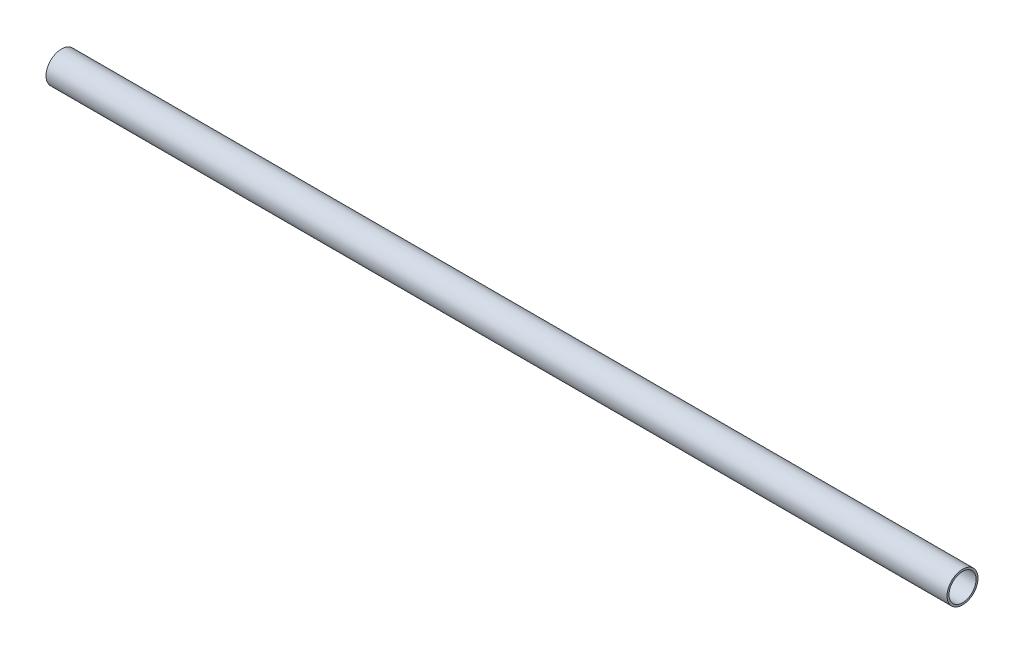
SolidWorks part; units mm, degrees
ref_plane "Ebene vorne" through (0, 0, 0) normal (0, 0, 1) x (1, 0, 0)
ref_plane "Ebene oben" through (0, 0, 0) normal (0, 1, 0) x (1, 0, 0)
ref_plane "Ebene rechts" through (0, 0, 0) normal (1, 0, 0) x (0, 0, -1)
sketch "Skizze1" plane through (0, 0, 0) normal (0, 0, 1) x (1, 0, 0)
  line L0 (0, 9.525) -> (554, 9.525)
  line L1 (554, 9.525) -> (554, 8.325)
  line L2 (554, 8.325) -> (0, 8.325)
  line L3 (0, 8.325) -> (0, 9.525)
  line L4 (0, 0) -> (554, 0) construction
  dimension "D1" = 554
  dimension "D2" = 9.525
  dimension "D3" = 8.325
revolve "Rotation1" add sketch "Skizze1" angle 360 about L4
sketch "Skizze2" plane through (0, 0, 0) normal (-1, 0, 0) x (0, 0, 1)
  line L0 (-8.6874, 0) -> (-6.6874, 0) construction
  line L1 (-8.6874, -0.3019) -> (-6.6874, -0.3019)
  line L2 (-8.6874, -0.3019) -> (-8.6874, 0.3019)
  line L3 (-8.6874, 0.3019) -> (-6.6874, 0.3019)
  line L4 (-6.6874, -0.3019) -> (-6.6874, 0.3019)
  point P6 (-2.7444, 0)
  dimension "D1" = 2
extrude "Aufsatz-Linear austragen1" add sketch "Skizze2" against normal blind 10
